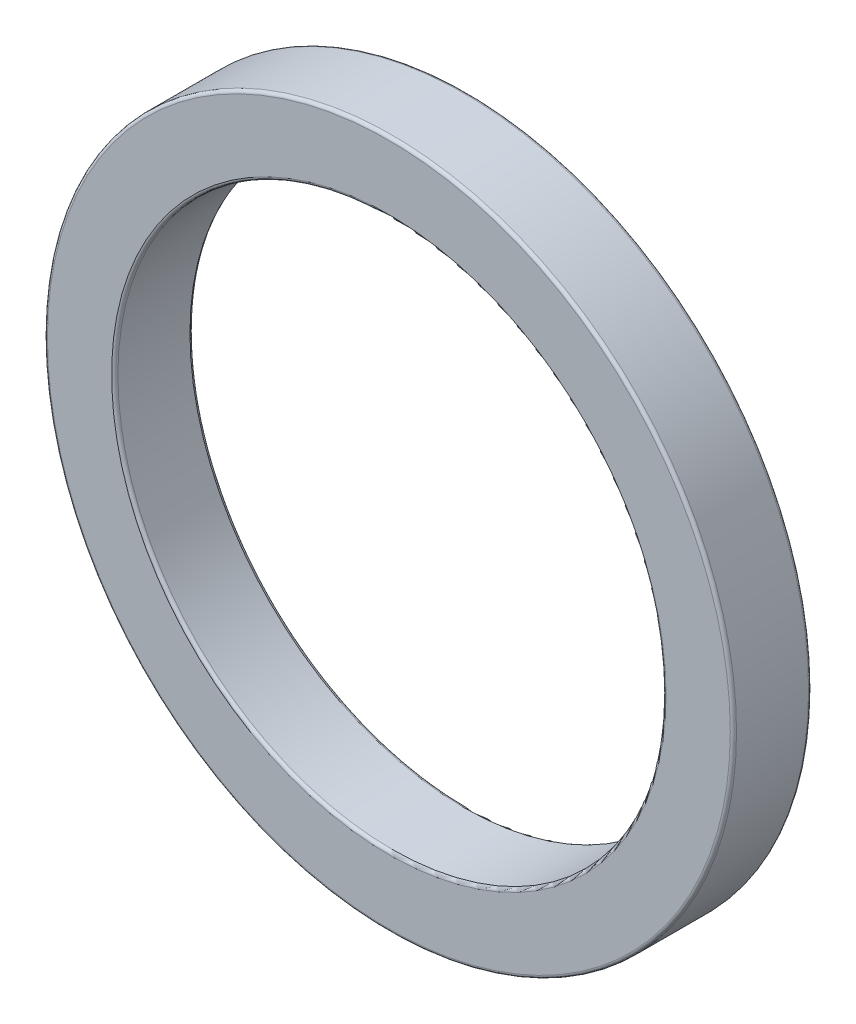
SolidWorks part; units mm, degrees
ref_plane "前视基准面" through (0, 0, 0) normal (0, 0, 1) x (1, 0, 0)
ref_plane "上视基准面" through (0, 0, 0) normal (0, 1, 0) x (1, 0, 0)
ref_plane "右视基准面" through (0, 0, 0) normal (1, 0, 0) x (0, 0, -1)
sketch "草图1" plane through (0, 0, 0) normal (0, 0, 1) x (1, 0, 0)
  circle A0 centre (0, 0) radius 17.5
  circle A1 centre (0, 0) radius 22
  dimension "D1" = 35
  dimension "D2" = 44
extrude "凸台-拉伸1" add sketch "草图1" along normal blind 5
fillet "圆角1" radius 0.2 4 edges at (17.5, 0, 0) (22, 0, 0) (22, 0, 5) (17.5, 0, 5)
